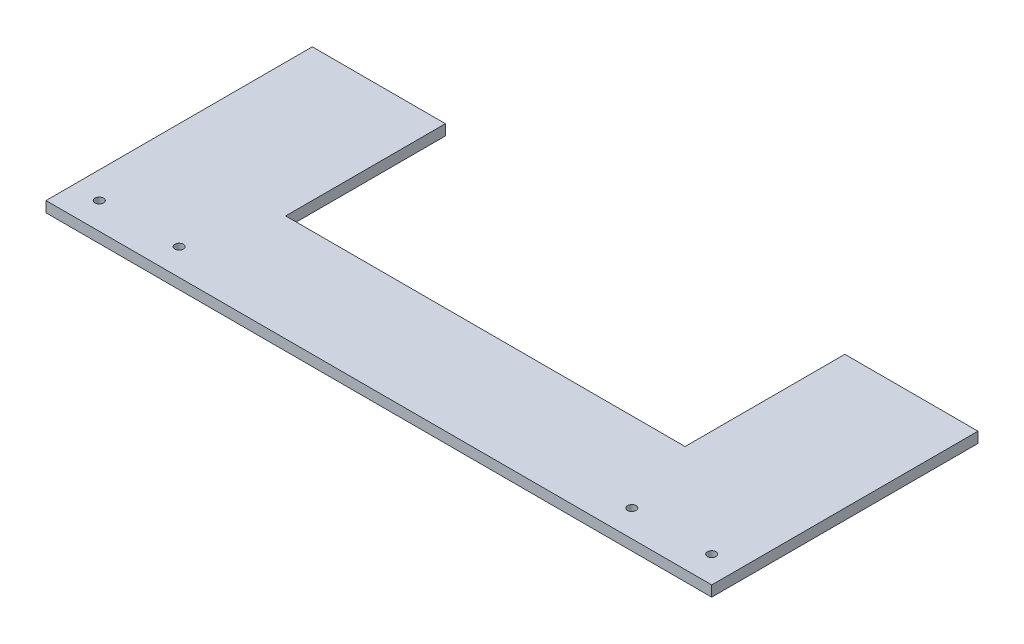
SolidWorks part; units mm, degrees
ref_plane "前视基准面" through (0, 0, 0) normal (0, 0, 1) x (1, 0, 0)
ref_plane "上视基准面" through (0, 0, 0) normal (0, 1, 0) x (1, 0, 0)
ref_plane "右视基准面" through (0, 0, 0) normal (1, 0, 0) x (0, 0, -1)
sketch "草图1" plane through (0, 0, 0) normal (0, 1, 0) x (1, 0, 0)
  line L0 (-75, 50) -> (-75, -50) construction
  line L1 (125, -50) -> (-125, -50)
  line L2 (125, -50) -> (125, 50)
  line L3 (125, 50) -> (-125, 50)
  line L4 (-125, -50) -> (-125, 50)
  line L5 (125, -50) -> (-125, 50) construction
  line L6 (125, 50) -> (-125, -50) construction
  line L8 (0, -50) -> (0, 50) construction
  circle A0 centre (-115, -40) radius 1.6
  circle A1 centre (-85, -40) radius 1.6
  circle A2 centre (85, -40) radius 1.6
  circle A3 centre (115, -40) radius 1.6
  point P0 (0, 0)
  dimension "D7" = 3.2
  dimension "D4" = 10
  dimension "D5" = 30
  dimension "D1" = 250
  dimension "D2" = 100
  dimension "D3" = 50
  dimension "D6" = 10
extrude "凸台-拉伸1" add sketch "草图1" along normal blind 4
sketch "草图2" plane through (0, 4, 0) normal (0, 1, 0) x (1, 0, 0)
  line L0 (0, -50) -> (0, 50) construction
  line L1 (-125, -50) -> (125, -50) construction
  line L2 (125, 50) -> (-125, 50) construction
  line L3 (75, 50) -> (75, -10)
  line L4 (75, -50.0077) -> (75, 74.7998) construction
  line L5 (75, -10) -> (-75, -10)
  line L6 (-75, 50) -> (75, 50)
  line L7 (-75, 50) -> (-75, -10)
  point P13 (0, -10)
  dimension "D1" = 60
extrude "切除-拉伸1" cut sketch "草图2" against normal through all
